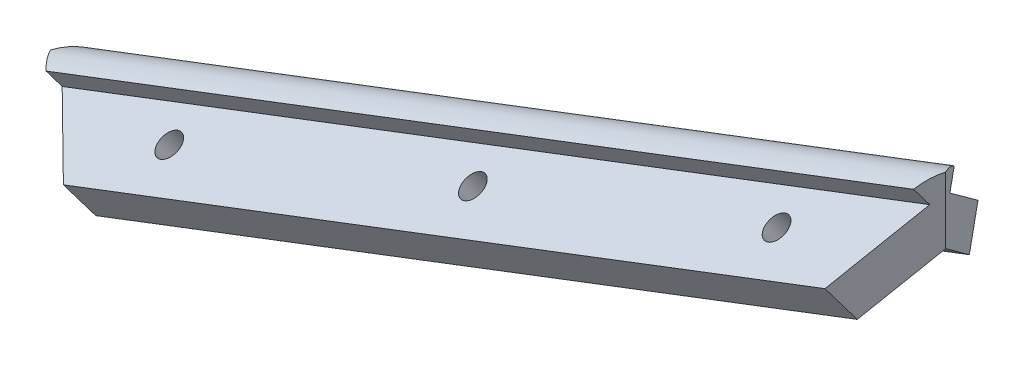
SolidWorks part; units mm, degrees
ref_plane "Front Plane" through (0, 0, 0) normal (0, 0, 1) x (1, 0, 0)
ref_plane "Top Plane" through (0, 0, 0) normal (0, 1, 0) x (1, 0, 0)
ref_plane "Right Plane" through (0, 0, 0) normal (1, 0, 0) x (0, 0, -1)
sketch "Sketch2" plane through (-61.5356, -23.5045, 0) normal (-0.9342, -0.3568, 0) x (0, 0, 1)
  line L0 (-1.3748, -3.9849) -> (-2.7769, -1.7162)
  line L1 (-1.3748, -3.9849) -> (-10.4661, -9.6037)
  line L2 (-104.12, -67.4849) -> (-1.3748, -3.9849) construction
  line L3 (-10.4661, -9.6037) -> (-7.6624, -14.1402)
  line L4 (-7.6624, -14.1402) -> (0, -9.4046)
  line L5 (0, -9.4046) -> (0, -0.9274)
  line L6 (-1.4527, -10.3024) -> (-0.283, -9.5795) construction
  line L7 (-1.5448, -7.5379) -> (-6.2234, -10.4294) construction
  arc A0 (-2.7769, -1.7162) -> (0, -0.9274) centre (0, -6.2094) cw
  dimension "D1" = 3.175
extrude "Boss-Extrude1" add sketch "Sketch2" against normal mid plane 152.4
mirror "Mirror4" about plane through (13.0041, -5.1002, 0) normal (0, 0, 1) of "Boss-Extrude1"
ref_plane "Plane1" through (-61.5356, -23.5045, 0) normal (0.9342, 0.3568, 0) x (0, 0, -1)
sketch "Sketch3" plane through (0, 0, 0) normal (0, 1, 0) x (1, 0, 0)
  line L0 (-6.0426, 10.4661) -> (0, 0)
  line L1 (0, 0) -> (-6.0426, -10.4661)
  line L2 (-6.0426, -10.4661) -> (57.4574, -10.4661)
  line L3 (57.4574, -10.4661) -> (57.4574, 10.4661)
  line L4 (57.4574, 10.4661) -> (-6.0426, 10.4661)
  line L8 (13.0751, -10.4661) -> (-129.2927, -10.4661) construction
  dimension "D1" = 120
  dimension "D2" = 63.5
extrude "Cut-Extrude2" cut sketch "Sketch3" against normal through all both and the other way through all
mirror "Mirror5" about plane through (-61.5356, -23.5045, 0) normal (0.9342, 0.3568, 0) of "Cut-Extrude2"
sketch "Sketch4" plane through (2.4282, -6.3572, 4.2058) normal (0.3035, -0.7947, 0.5257) x (0.9528, 0.2531, -0.1675)
  line L0 (-22.0278, -11.2082) -> (-22.5354, -12.7126) construction
  line L1 (-65.6078, -19.9596) -> (-66.1154, -21.464) construction
  line L2 (-109.1878, -28.7109) -> (-109.6954, -30.2153) construction
  line L3 (-22.0278, -11.2082) -> (-22.5354, -12.7126) construction
  line L4 (-65.6078, -19.9596) -> (-66.1154, -21.464) construction
  line L5 (-109.1878, -28.7109) -> (-109.6954, -30.2153) construction
  line L7 (-109.6954, -30.2153) -> (-107.5974, -32.5989)
  line L8 (-107.5974, -32.5989) -> (-104.4841, -31.9737)
  line L9 (-104.4841, -31.9737) -> (-103.4689, -28.965)
  line L10 (-103.4689, -28.965) -> (-105.5669, -26.5814)
  line L11 (-105.5669, -26.5814) -> (-108.6802, -27.2066)
  line L12 (-108.6802, -27.2066) -> (-109.6954, -30.2153)
  line L13 (-66.1154, -21.464) -> (-64.0174, -23.8476)
  line L14 (-64.0174, -23.8476) -> (-60.9041, -23.2224)
  line L15 (-60.9041, -23.2224) -> (-59.8889, -20.2136)
  line L16 (-59.8889, -20.2136) -> (-61.9869, -17.83)
  line L17 (-61.9869, -17.83) -> (-65.1002, -18.4552)
  line L18 (-65.1002, -18.4552) -> (-66.1154, -21.464)
  line L19 (-22.5354, -12.7126) -> (-20.4374, -15.0962)
  line L20 (-20.4374, -15.0962) -> (-17.3241, -14.471)
  line L21 (-17.3241, -14.471) -> (-16.3089, -11.4622)
  line L22 (-16.3089, -11.4622) -> (-18.4069, -9.0787)
  line L23 (-18.4069, -9.0787) -> (-21.5202, -9.7038)
  line L24 (-21.5202, -9.7038) -> (-22.5354, -12.7126)
  circle A0 centre (-106.5821, -29.5901) radius 2.75 construction
  circle A1 centre (-63.0021, -20.8388) radius 2.75 construction
  circle A2 centre (-19.4221, -12.0874) radius 2.75 construction
  circle A3 centre (-106.5821, -29.5901) radius 1.7145
  circle A4 centre (-63.0021, -20.8388) radius 1.7145
  circle A5 centre (-19.4221, -12.0874) radius 1.7145
  point P0 (-19.4221, -12.0874)
  point P2 (-106.5821, -29.5901)
  point P4 (-63.0021, -20.8388)
  dimension "D1" = 3.429
extrude "Cut-Extrude3" cut sketch "Sketch4" against normal blind 2.5
sketch "Sketch6" plane through (2.4282, -6.3572, 4.2058) normal (0.3035, -0.7947, 0.5257) x (0.9528, 0.2531, -0.1675)
  circle A1 centre (-106.5821, -29.5901) radius 1.7145
  circle A2 centre (-106.5821, -29.5901) radius 1.7145
  circle A3 centre (-63.0021, -20.8388) radius 1.7145
  circle A4 centre (-63.0021, -20.8388) radius 1.7145
  circle A5 centre (-19.4221, -12.0874) radius 1.7145
  circle A6 centre (-19.4221, -12.0874) radius 1.7145
  dimension "D1" = 0
  dimension "D2" = 0
  dimension "D3" = 0
extrude "Cut-Extrude4" cut sketch "Sketch6" against normal through all
mirror "Mirror6" about plane through (0, 0, 0) normal (0, 0, 1) of "Cut-Extrude4", "Cut-Extrude3"
